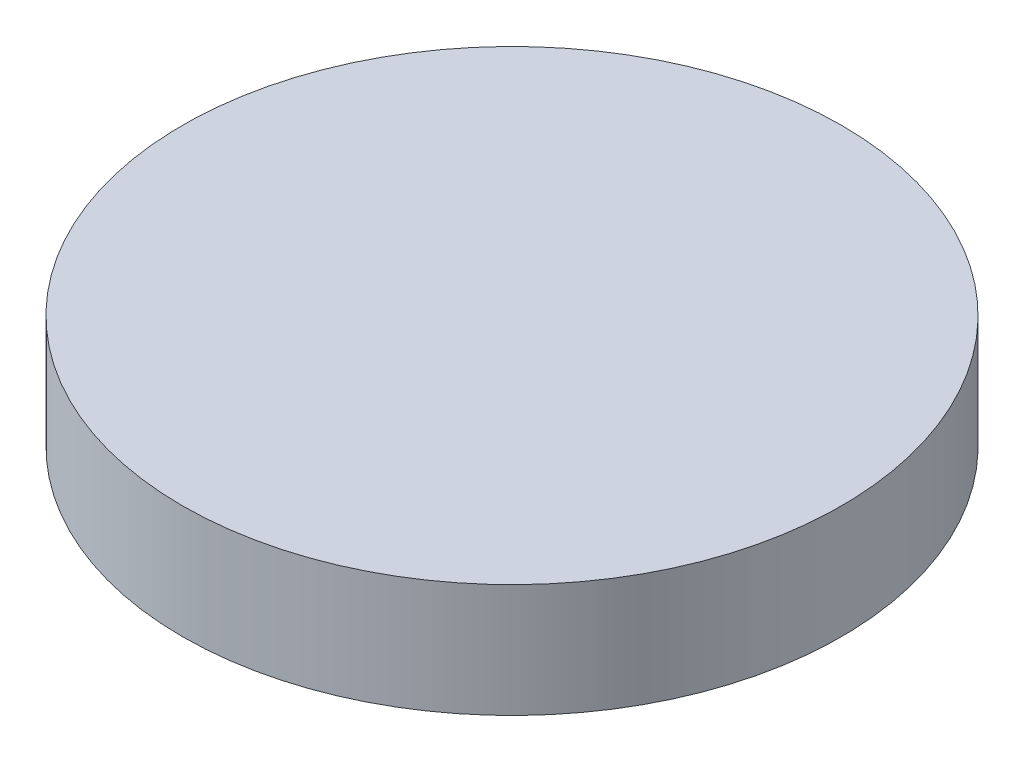
SolidWorks part; units mm, degrees
ref_plane "Front Plane" through (0, 0, 0) normal (0, 0, 1) x (1, 0, 0)
ref_plane "Top Plane" through (0, 0, 0) normal (0, 1, 0) x (1, 0, 0)
ref_plane "Right Plane" through (0, 0, 0) normal (1, 0, 0) x (0, 0, -1)
ref_plane "Plane1"
sketch "Sketch1" plane through (0, 0, 0) normal (0, 1, 0) x (-1, 0, 0)
  circle A0 centre (0, 0) radius 2.9075
extrude "Extrusion1" add sketch "Sketch1" along normal blind 1
